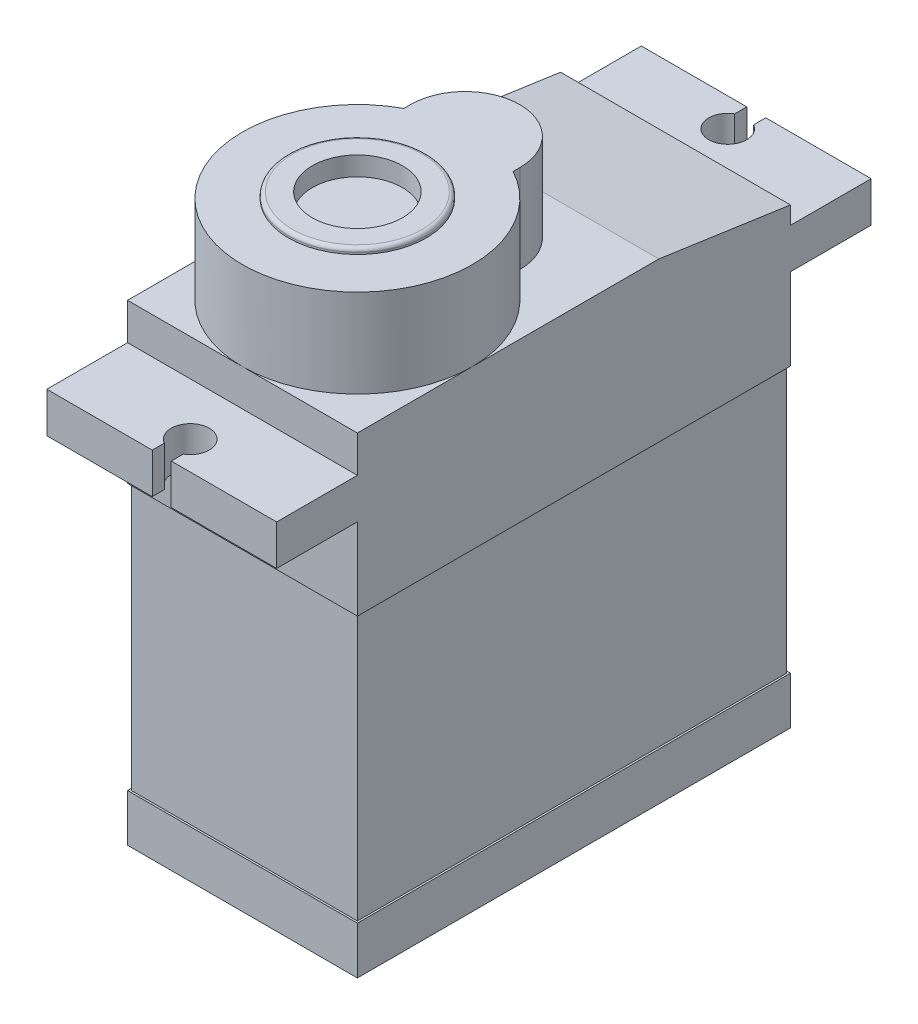
SolidWorks part; units mm, degrees
ref_plane "Front Plane" through (0, 0, 0) normal (0, 0, 1) x (1, 0, 0)
ref_plane "Top Plane" through (0, 0, 0) normal (0, 1, 0) x (1, 0, 0)
ref_plane "Right Plane" through (0, 0, 0) normal (1, 0, 0) x (0, 0, -1)
sketch "Sketch1" plane through (0, 0, 0) normal (0, 1, 0) x (1, 0, 0)
  line L1 (6.05, -11.4) -> (-6.05, -11.4)
  line L2 (6.05, -11.4) -> (6.05, 11.4)
  line L3 (6.05, 11.4) -> (-6.05, 11.4)
  line L4 (-6.05, -11.4) -> (-6.05, 11.4)
  line L5 (6.05, -11.4) -> (-6.05, 11.4) construction
  line L6 (6.05, 11.4) -> (-6.05, -11.4) construction
  point P0 (0, 0)
  dimension "D1" = 22.8
  dimension "D2" = 12.1
extrude "Boss-Extrude1" add sketch "Sketch1" along normal blind 24.85
sketch "Sketch2" plane through (-6.05, 0, 0) normal (-1, 0, 0) x (0, 0, 1)
  line L1 (-11.4, 23.85) -> (-4.4718, 24.85)
  line L2 (-11.4, 24.85) -> (-11.4, 0) construction
  line L3 (-11.4, 24.85) -> (11.4, 24.85) construction
  line L4 (-4.4718, 24.85) -> (11.4, 24.85)
  line L5 (11.4, 24.85) -> (11.4, 0)
  line L6 (11.4, 0) -> (-11.4, 0)
  line L7 (-11.4, 0) -> (-11.4, 23.85)
  dimension "D1" = 23.85
  dimension "D2" = 7
extrude "Cut-Extrude1" cut sketch "Sketch2" against normal blind 24.85 flip side to cut
sketch "Sketch3" plane through (0, 24.85, 0) normal (0, 1, 0) x (1, 0, 0)
  line L0 (-6.05, -11.4) -> (6.05, -11.4) construction
  line L1 (-1.2801, 3.2) -> (1.4091, 3.2) construction
  line L2 (2.875, 0.325) -> (2.875, -0.0268)
  line L3 (-2.875, 0.325) -> (-2.875, -0.0268)
  line L4 (0, 3.2) -> (0, -11.4) construction
  line L5 (-6.05, 4.4718) -> (-6.05, -11.4) construction
  line L6 (6.05, -11.4) -> (6.05, 4.4718) construction
  circle A0 centre (0, -5.35) radius 6.05
  circle A1 centre (0, 0.325) radius 2.875
  dimension "D2" = 5.75
  dimension "D1" = 14.6
extrude "Boss-Extrude2" add sketch "Sketch3" along normal offset from surface (4.65 mm away) 29.5 contours A1 A0 | A1 A0 L2 | A1 L3 A0 | A0 A1 | A0 A1 up to face at (0, 0, 0)
sketch "Sketch4" plane through (0, 0, 0) normal (0, 1, 0) x (1, 0, 0)
  line L0 (-6.05, 11.4) -> (-6.05, -11.4) construction
  line L1 (-6.05, 0) -> (6.05, 0) construction
  line L2 (6.05, -5.35) -> (6.05, 4.4718) construction
  line L3 (0, 15.15) -> (0, 15.65) construction
  line L4 (-6.05, 11.4) -> (6.05, 11.4)
  line L5 (-6.05, 11.4) -> (-6.05, 15.65)
  line L6 (-6.05, 15.65) -> (6.05, 15.65)
  line L7 (6.05, 11.4) -> (6.05, 15.65)
  line L8 (-6.05, -11.4) -> (6.05, -11.4)
  line L9 (-6.05, -11.4) -> (-6.05, -15.65)
  line L10 (-6.05, -15.65) -> (6.05, -15.65)
  line L11 (6.05, -11.4) -> (6.05, -15.65)
  line L12 (-0.5, 15.65) -> (-0.5, 15.016)
  line L13 (0.5, 15.016) -> (0.5, 15.65)
  line L14 (6.05, 4.4718) -> (6.05, 11.4) construction
  line L15 (6.05, -11.4) -> (6.05, -5.35) construction
  line L16 (0.5, -15.016) -> (0.5, -15.65)
  line L17 (-0.5, -15.65) -> (-0.5, -15.016)
  circle A0 centre (0, 14.15) radius 1
  circle A1 centre (0, -14.15) radius 1
  dimension "D2" = 2
  dimension "D1" = 4.25
  dimension "D3" = 1.5
  dimension "D4" = 0.5
extrude "Boss-Extrude3" add sketch "Sketch4" along normal blind 2.12 from offset 20.8 contours A0 L12 L6 L5 L4 L7 L13 | L17 A1 L16 L10 L11 L8 L9
sketch "Sketch6" plane through (0, 0, 0) normal (0, -1, 0) x (1, 0, 0)
  line L0 (5.95, 11.3) -> (-5.95, 11.3)
  line L1 (-5.95, 11.3) -> (-5.95, -11.3)
  line L2 (-5.95, -11.3) -> (5.95, -11.3)
  line L3 (5.95, -11.3) -> (5.95, 11.3)
  line L4 (-6.05, 11.4) -> (-6.05, -11.4)
  line L5 (-6.05, -11.4) -> (6.05, -11.4)
  line L6 (6.05, -11.4) -> (6.05, 11.4)
  line L7 (6.05, 11.4) -> (-6.05, 11.4)
  line L8 (-6.05, 11.4) -> (-6.05, -11.4)
  line L9 (-6.05, -11.4) -> (6.05, -11.4)
  line L10 (6.05, -11.4) -> (6.05, 11.4)
  line L11 (6.05, 11.4) -> (-6.05, 11.4)
  dimension "D1" = 0
  dimension "D2" = 0.1
extrude "Cut-Extrude2" cut sketch "Sketch6" against normal blind 14 from offset 2.5 offset against normal yes
sketch "Sketch7" plane through (0, 24.9751, -3.6048) normal (0, 0.9897, -0.1429) x (1, 0, 0)
  line L0 (-20.8911, -66.3638) -> (-215.5578, -66.3638) construction
  line L1 (12, 23) -> (60, 23) construction
  line L2 (-6.8904, -60.1027) -> (-185.5571, -60.1027) construction
  line L3 (-321.6038, 87.1261) -> (-142.9372, 87.1261) construction
  line L4 (-36.2186, -75.2837) -> (-214.8853, -75.2837) construction
sketch "Sketch8" plane through (0, 29.5, 0) normal (0, 1, 0) x (1, 0, 0)
  circle A0 centre (0, -5.35) radius 3.625
  dimension "D1" = 7.25
extrude "Boss-Extrude5" add sketch "Sketch8" along normal blind 0.3
fillet "Fillet1" radius 0.2 1 edges at (0, 29.8, 8.975)
sketch "Sketch9" plane through (0, 29.8, 0) normal (0, 1, 0) x (1, 0, 0)
  circle A0 centre (0, -5.35) radius 2.375
  dimension "D1" = 4.75
extrude "Cut-Extrude3" cut sketch "Sketch9" against normal blind 1
